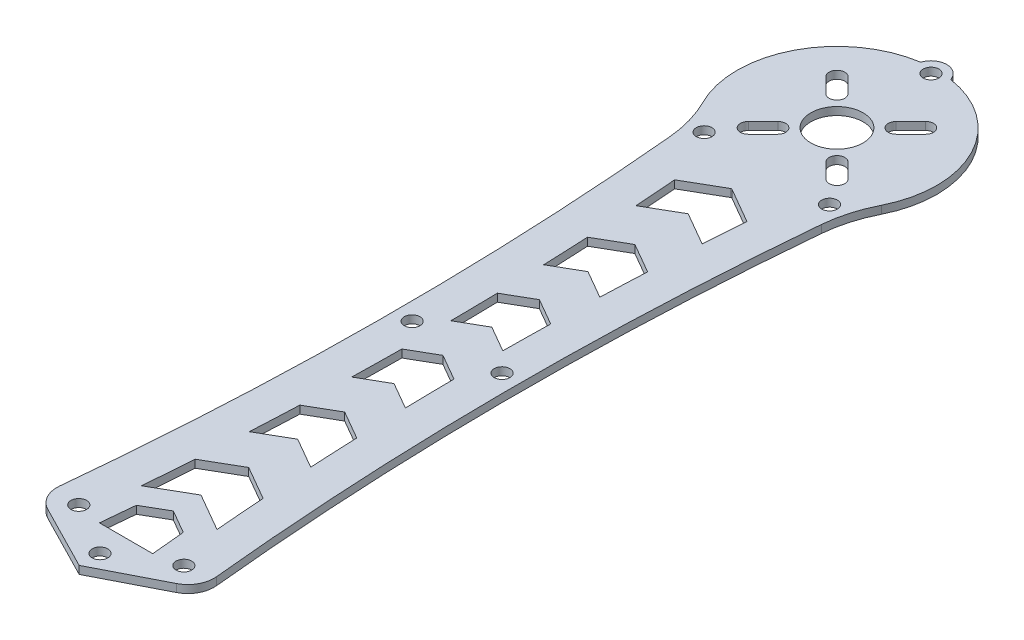
SolidWorks part; units mm, degrees
ref_plane "前基準面" through (0, 0, 0) normal (0, 0, 1) x (1, 0, 0)
ref_plane "上基準面" through (0, 0, 0) normal (0, 1, 0) x (1, 0, 0)
ref_plane "右基準面" through (0, 0, 0) normal (1, 0, 0) x (0, 0, -1)
sketch "草圖1" plane through (0, 0, 0) normal (0, 1, 0) x (1, 0, 0)
  line L0 (-45.7929, 39.3947) -> (118.2116, 38.9653) construction
  line L1 (0, -25.4446) -> (0, 154.6519) construction
  line L2 (0, 14.0424) -> (-4.4911, 11.4495)
  line L3 (0, -3.9809) -> (12.3191, 2.3288)
  line L4 (0, 112.5321) -> (-6.334, 108.8752)
  line L5 (0, 112.5321) -> (6.334, 108.8752)
  line L6 (-46.5392, 127.5836) -> (-7.6665, 127.5836) construction
  line L7 (0, 102.3449) -> (5.754, 99.0229)
  line L8 (0.1364, 120.7804) -> (6.9215, 116.863)
  line L9 (0, 84.0727) -> (5.1071, 81.1241)
  line L10 (0, 74.9698) -> (4.9796, 72.0949)
  line L11 (0, 65.6198) -> (4.9879, 62.74)
  line L12 (0, 93.3641) -> (5.3719, 90.2626)
  line L13 (0, 56.2626) -> (5.1412, 53.2943)
  line L14 (0, 46.8277) -> (5.447, 43.6829)
  line L15 (0, 37.8313) -> (5.884, 34.4342)
  line L16 (0, 28.4608) -> (6.4948, 24.7111)
  line L17 (0, 19.3311) -> (7.2473, 15.1468)
  line L18 (0, 14.0424) -> (4.4911, 11.4495)
  line L19 (-5.1012, 5.0028) -> (5.1012, 5.0028)
  line L20 (0, 19.3311) -> (-7.2473, 15.1468)
  line L21 (0, 28.4608) -> (-6.4948, 24.7111)
  line L22 (0, 37.8313) -> (-5.884, 34.4342)
  line L23 (0, 46.8277) -> (-5.447, 43.6829)
  line L24 (0, 56.2626) -> (-5.1412, 53.2943)
  line L25 (0, 65.6198) -> (-4.9879, 62.74)
  line L26 (0, 74.9698) -> (-4.9796, 72.0949)
  line L27 (0, 84.0727) -> (-5.1071, 81.1241)
  line L28 (0, 93.3641) -> (-5.3719, 90.2626)
  line L29 (0, 102.3449) -> (-5.754, 99.0229)
  line L30 (-4.4911, 11.4495) -> (-5.1012, 5.0028)
  line L31 (-0.1364, 120.7804) -> (-6.9215, 116.863)
  line L32 (0, -3.9809) -> (-12.3191, 2.3288)
  line L33 (4.4911, 11.4495) -> (5.1012, 5.0028)
  line L34 (-26.7622, 114.2378) -> (26.7623, 167.7623) construction
  line L35 (26.7622, 114.2378) -> (-26.7623, 167.7623) construction
  line L36 (0, 3.8839) -> (-7.9144, 7.9376) construction
  line L37 (0, 3.8839) -> (7.9144, 7.9376) construction
  line L38 (-5.6569, 146.6569) -> (-8.4853, 149.4853) construction
  line L39 (-6.7175, 145.5962) -> (-9.5459, 148.4246)
  line L40 (-4.5962, 147.7175) -> (-7.4246, 150.5459)
  line L41 (5.6569, 146.6569) -> (8.4853, 149.4853) construction
  line L42 (6.7175, 145.5962) -> (9.5459, 148.4246)
  line L43 (4.5962, 147.7175) -> (7.4246, 150.5459)
  line L44 (-5.6569, 135.3431) -> (-8.4853, 132.5147) construction
  line L45 (-4.5962, 134.2825) -> (-7.4246, 131.4541)
  line L46 (-6.7175, 136.4038) -> (-9.5459, 133.5754)
  line L47 (5.6569, 135.3431) -> (8.4853, 132.5147) construction
  line L48 (4.5962, 134.2825) -> (7.4246, 131.4541)
  line L49 (6.7175, 136.4038) -> (9.5459, 133.5754)
  arc A0 (-6.7175, 145.5962) -> (-4.5962, 147.7175) centre (-5.6569, 146.6569) ccw
  circle A1 centre (-12, 127.5836) radius 1.5
  circle A2 centre (12, 127.5836) radius 1.5
  circle A3 centre (8.6, 68.3254) radius 1.5
  circle A4 centre (-8.6, 68.3254) radius 1.5
  circle A5 centre (10.05, 6) radius 1.5
  circle A6 centre (-10.05, 6) radius 1.5
  circle A7 centre (0, 159) radius 1.5
  circle A8 centre (0, 0) radius 1.5
  circle A9 centre (0, 141) radius 5
  arc A10 (7.5514, 124.1751) -> (7.9144, 7.9376) centre (617.3178, 67.9598) ccw construction
  arc A11 (-5.754, 99.0229) -> (-5.3719, 90.2626) centre (-617.3178, 67.9598) cw
  arc A12 (5.754, 99.0229) -> (5.3719, 90.2626) centre (617.3178, 67.9598) ccw
  arc A13 (-12.3191, 2.3288) -> (-15.0145, 7.2803) centre (-10.0397, 6.7791) cw
  arc A14 (0.1364, 120.7804) -> (-0.1364, 120.7804) centre (0, 120.5442) ccw
  arc A15 (14.5218, 123.5325) -> (15.0145, 7.2803) centre (617.3178, 67.9598) ccw
  arc A16 (17.067, 132.4252) -> (2.8669, 159.8836) centre (0, 141) ccw
  arc A17 (12.3191, 2.3288) -> (15.0145, 7.2803) centre (10.0397, 6.7791) ccw
  arc A18 (14.5218, 123.5325) -> (17.067, 132.4252) centre (39.3167, 121.2466) cw
  arc A19 (-14.5218, 123.5325) -> (-17.067, 132.4252) centre (-39.3167, 121.2466) ccw
  arc A20 (6.9215, 116.863) -> (6.334, 108.8752) centre (617.3178, 67.9598) ccw
  arc A21 (-14.5218, 123.5325) -> (-15.0145, 7.2803) centre (-617.3178, 67.9598) cw
  arc A22 (7.9144, 7.9376) -> (7.9144, 7.9376) centre (7.9144, 7.9376) ccw
  arc A23 (-7.9144, 7.9376) -> (-7.9144, 7.9376) centre (-7.9144, 7.9376) cw
  arc A24 (-6.9215, 116.863) -> (-6.334, 108.8752) centre (-617.3178, 67.9598) cw
  arc A25 (-7.5514, 124.1751) -> (-7.9144, 7.9376) centre (-617.3178, 67.9598) cw construction
  arc A26 (5.1071, 81.1241) -> (4.9796, 72.0949) centre (617.3178, 67.9598) ccw
  arc A27 (-5.1071, 81.1241) -> (-4.9796, 72.0949) centre (-617.3178, 67.9598) cw
  arc A28 (10.8121, 135.5678) -> (-10.8121, 135.5678) centre (0, 141) ccw construction
  arc A29 (-7.5514, 124.1751) -> (-10.8121, 135.5678) centre (-39.3167, 121.2466) ccw construction
  arc A30 (7.5514, 124.1751) -> (10.8121, 135.5678) centre (39.3167, 121.2466) cw construction
  arc A31 (-4.9879, 62.74) -> (-5.1412, 53.2943) centre (-617.3178, 67.9598) cw
  arc A32 (4.9879, 62.74) -> (5.1412, 53.2943) centre (617.3178, 67.9598) ccw
  arc A33 (-5.447, 43.6829) -> (-5.884, 34.4342) centre (-617.3178, 67.9598) cw
  arc A34 (5.447, 43.6829) -> (5.884, 34.4342) centre (617.3178, 67.9598) ccw
  arc A35 (-6.4948, 24.7111) -> (-7.2473, 15.1468) centre (-617.3178, 67.9598) cw
  arc A36 (6.4948, 24.7111) -> (7.2473, 15.1468) centre (617.3178, 67.9598) ccw
  arc A37 (2.8669, 159.8836) -> (-2.8669, 159.8836) centre (0, 159) ccw
  circle A38 centre (0, 159) radius 3 construction
  arc A39 (-2.8669, 159.8836) -> (-17.067, 132.4252) centre (0, 141) ccw
  arc A40 (17.067, 132.4252) -> (-17.067, 132.4252) centre (0, 141) ccw construction
  arc A41 (-7.4246, 150.5459) -> (-9.5459, 148.4246) centre (-8.4853, 149.4853) ccw
  arc A42 (6.7175, 145.5962) -> (4.5962, 147.7175) centre (5.6569, 146.6569) cw
  arc A43 (7.4246, 150.5459) -> (9.5459, 148.4246) centre (8.4853, 149.4853) cw
  arc A44 (-4.5962, 134.2825) -> (-6.7175, 136.4038) centre (-5.6569, 135.3431) ccw
  arc A45 (-9.5459, 133.5754) -> (-7.4246, 131.4541) centre (-8.4853, 132.5147) ccw
  arc A46 (4.5962, 134.2825) -> (6.7175, 136.4038) centre (5.6569, 135.3431) cw
  arc A47 (9.5459, 133.5754) -> (7.4246, 131.4541) centre (8.4853, 132.5147) cw
  point P27 (0, 141)
  point P42 (0, 115.0816)
  point P61 (-7.0711, 148.0711)
  point P69 (-11.6194, 152.6194)
  point P71 (-6.6656, 147.6656)
  point P75 (7.0711, 148.0711)
  point P77 (0, 5.0028)
  point P83 (-7.0711, 133.9289)
  point P130 (7.0711, 133.9289)
  point P136 (-8.9949, 132.0051)
  dimension "D3" = 3
  dimension "D4" = 3
  dimension "D5" = 3
  dimension "D6" = 3
  dimension "D7" = 3
  dimension "D8" = 7
  dimension "D9" = 141
  dimension "D10" = 5
  dimension "D11" = 24
  dimension "D12" = 120
  dimension "D13" = 0.2728
  dimension "D14" = 38.2
  dimension "D15" = 20.1
  dimension "D16" = 24.9
  dimension "D22" = 10
  dimension "D24" = 3
  dimension "D17" = 6
  dimension "D18" = 17.2
  dimension "D20" = 18
  dimension "D21" = 18
  dimension "D23" = 90
  dimension "D25" = 10
  dimension "D26" = 4
  dimension "D19" = 1.5
extrude "填料-伸長1" add sketch "草圖1" along normal blind 1.5 contours A19 A21 A13 L32 L3 A17 A15 A18 A16 A7 A27 L27 L9 A26 L10 L26 A24 L31 A14 L8 A20 L5 L4 L7 A12 L12 L28 A11 L29 A6 A5 A2 A1 L18 L33 L19 L30 L2 A3 A4
